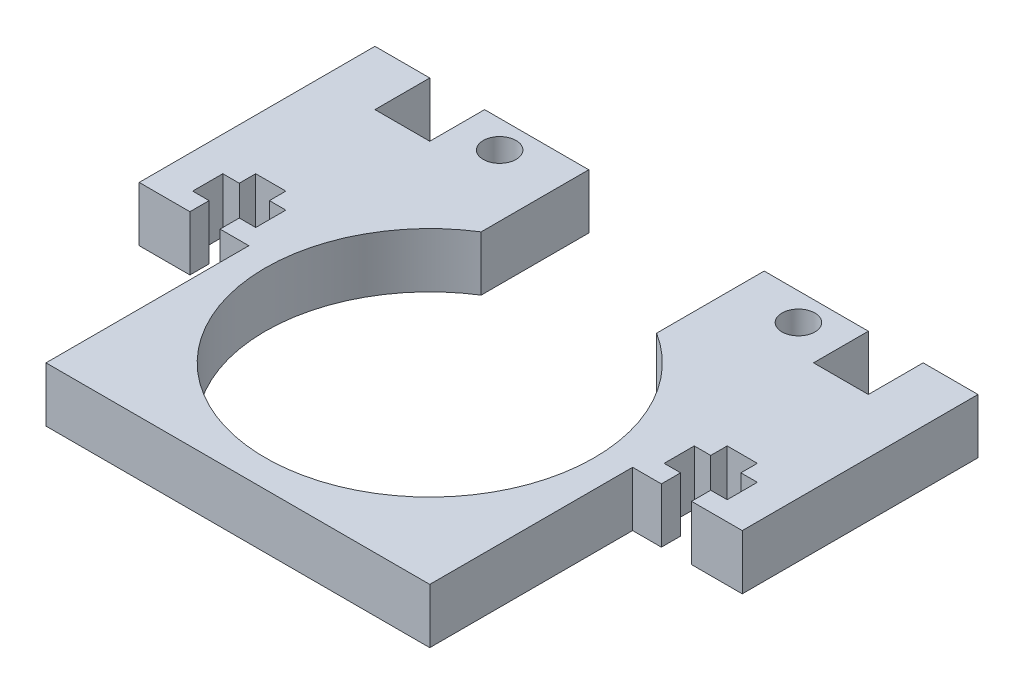
SolidWorks part; units mm, degrees
material "Balsa"
ref_plane "Plan de face" through (0, 0, 0) normal (0, 0, 1) x (1, 0, 0)
ref_plane "Plan de dessus" through (0, 0, 0) normal (0, 1, 0) x (1, 0, 0)
ref_plane "Plan de droite" through (0, 0, 0) normal (1, 0, 0) x (0, 0, -1)
sketch "Esquisse1" plane through (0, 0, 0) normal (0, 1, 0) x (1, 0, 0)
  line L1 (-17.5, 17.5) -> (17.5, 17.5)
  line L2 (-17.5, 17.5) -> (-17.5, -17.5)
  line L3 (-17.5, -17.5) -> (17.5, -17.5)
  line L4 (17.5, 17.5) -> (17.5, -17.5)
  dimension "D3" = 17.5
  dimension "D1" = 35
  dimension "D2" = 35
  dimension "D4" = 17.5
extrude "Boss.-Extru.1" add sketch "Esquisse1" along normal blind 5
sketch "Esquisse2" plane through (0, 5, 0) normal (0, 1, 0) x (1, 0, 0)
  line L1 (17.5, 17.5) -> (-17.5, 17.5) construction
  line L2 (-27.5, 17.5) -> (27.5, 17.5)
  line L3 (-27.5, 17.5) -> (-27.5, 22.5)
  line L4 (-27.5, 22.5) -> (27.5, 22.5)
  line L5 (27.5, 17.5) -> (27.5, 22.5)
  line L6 (-17.5, 17.5) -> (-17.5, -17.5) construction
  dimension "D1" = 5
  dimension "D2" = 55
  dimension "D3" = 10
sketch "Esquisse3" plane through (0, 5, 0) normal (0, 1, 0) x (1, 0, 0)
  circle A0 centre (0, 0) radius 15
  dimension "D1" = 30
extrude "Enlèv. mat.-Extru.1" cut sketch "Esquisse3" against normal blind 5
ref_plane "Plan1" through (-17.5, 5, -17.5) normal (0, 0, 1) x (1, 0, 0)
sketch "Esquisse8" plane through (0, 5, 0) normal (0, 1, 0) x (1, 0, 0)
  line L1 (-8, 22.5) -> (8, 22.5)
  line L2 (-8, 22.5) -> (-8, 12.6886)
  line L3 (-8, 12.6886) -> (8, 12.6886)
  line L4 (8, 22.5) -> (8, 12.6886)
  line L5 (17.5, 17.5) -> (-17.5, 17.5) construction
  circle A0 centre (0, 0) radius 15 construction
  dimension "D1" = 16
  dimension "D2" = 8
  dimension "D3" = 5
sketch "Esquisse5" plane through (0, 5, 0) normal (0, 1, 0) x (1, 0, 0)
  line L0 (-17.5, 17.5) -> (-17.5, -17.5) construction
  line L1 (-17.5, 17.5) -> (-27.5, 17.5)
  line L2 (-17.5, 17.5) -> (-17.5, 1)
  line L3 (-17.5, 1) -> (-27.5, 1)
  line L4 (-27.5, 17.5) -> (-27.5, 1)
  dimension "D1" = 10
  dimension "D2" = 16.5
  dimension "D3" = 1
extrude "Boss.-Extru.3" add sketch "Esquisse5" against normal blind 5
mirror "Symétrie1" about plane through (0, 0, 0) normal (1, 0, 0) of "Boss.-Extru.3"
sketch "Esquisse7" plane through (0, 5, 0) normal (0, 1, 0) x (1, 0, 0)
  line L0 (-22.875, 1) -> (-22.875, 2.75)
  line L1 (-27.5, 1) -> (-17.5, 1) construction
  line L2 (-22.875, 2.75) -> (-24.375, 2.75)
  line L3 (-24.375, 2.75) -> (-24.375, 5.5)
  line L4 (-24.375, 5.5) -> (-22.875, 5.5)
  line L5 (-22.875, 5.5) -> (-22.875, 7)
  line L6 (-22.875, 7) -> (-20.125, 7)
  line L7 (-20.125, 7) -> (-20.125, 5.5)
  line L8 (-20.125, 5.5) -> (-18.625, 5.5)
  line L9 (-18.625, 5.5) -> (-18.625, 2.75)
  line L10 (-18.625, 2.75) -> (-20.125, 2.75)
  line L11 (-20.125, 2.75) -> (-20.125, 1)
  line L12 (-20.125, 1) -> (-22.875, 1)
  line L17 (-17.5, 1) -> (-17.5, -17.5) construction
  dimension "D1" = 2.75
  dimension "D2" = 2.75
  dimension "D3" = 5.75
  dimension "D4" = 1.5
  dimension "D5" = 1.5
  dimension "D6" = 1.75
  dimension "D7" = 2.75
  dimension "D8" = 6
  dimension "D9" = 2.75
  dimension "D10" = 1.75
  dimension "D11" = 2.625
extrude "Enlèv. mat.-Extru.3" cut sketch "Esquisse7" against normal blind 10 contours L6 L7 L8 L9 L10 L11 L12 L0 L2 L3 L4 L5
mirror "Symétrie2" about plane through (0, 0, 0) normal (1, 0, 0) of "Enlèv. mat.-Extru.3"
extrude "Boss.-Extru.4" add sketch "Esquisse2" against normal blind 5
extrude "Enlèv. mat.-Extru.5" cut sketch "Esquisse8" against normal blind 5
sketch "Esquisse9" plane through (0, 5, 0) normal (0, 1, 0) x (1, 0, 0)
  line L0 (-8, 22.5) -> (-27.5, 22.5) construction
  line L1 (-22.5, 22.5) -> (-17.5, 22.5)
  line L2 (-22.5, 22.5) -> (-22.5, 17.5)
  line L3 (-22.5, 17.5) -> (-17.5, 17.5)
  line L4 (-17.5, 22.5) -> (-17.5, 17.5)
  line L5 (-22.5875, 17.5) -> (-12.4125, 17.5) construction
  line L7 (-27.5, 22.5) -> (-27.5, 1) construction
  line L9 (27.5, 22.5) -> (8, 22.5) construction
  line L10 (22.5, 22.5) -> (17.5, 22.5)
  line L11 (22.5, 22.5) -> (22.5, 17.5)
  line L12 (22.5, 17.5) -> (17.5, 17.5)
  line L13 (17.5, 22.5) -> (17.5, 17.5)
  line L14 (27.5, 22.5) -> (27.5, 1) construction
  dimension "D1" = 5
  dimension "D2" = 5
  dimension "D3" = 5
  dimension "D4" = 5
  dimension "D5" = 5
extrude "Enlèv. mat.-Extru.6" cut sketch "Esquisse9" against normal blind 5
sketch "Esquisse10" plane through (0, 5, 0) normal (0, 1, 0) x (1, 0, 0)
  line L0 (-27.5, 22.5) -> (-27.5, 1) construction
  line L1 (-8, 22.5) -> (-17.5, 22.5) construction
  line L2 (0, 2.8494) -> (0, 11.63) construction
  circle A0 centre (-13.625, 20) radius 1.5
  circle A1 centre (13.625, 20) radius 1.5
  dimension "D2" = 3
  dimension "D1" = 13.875
  dimension "D3" = 2.5
extrude "Enlèv. mat.-Extru.7" cut sketch "Esquisse10" against normal through all
